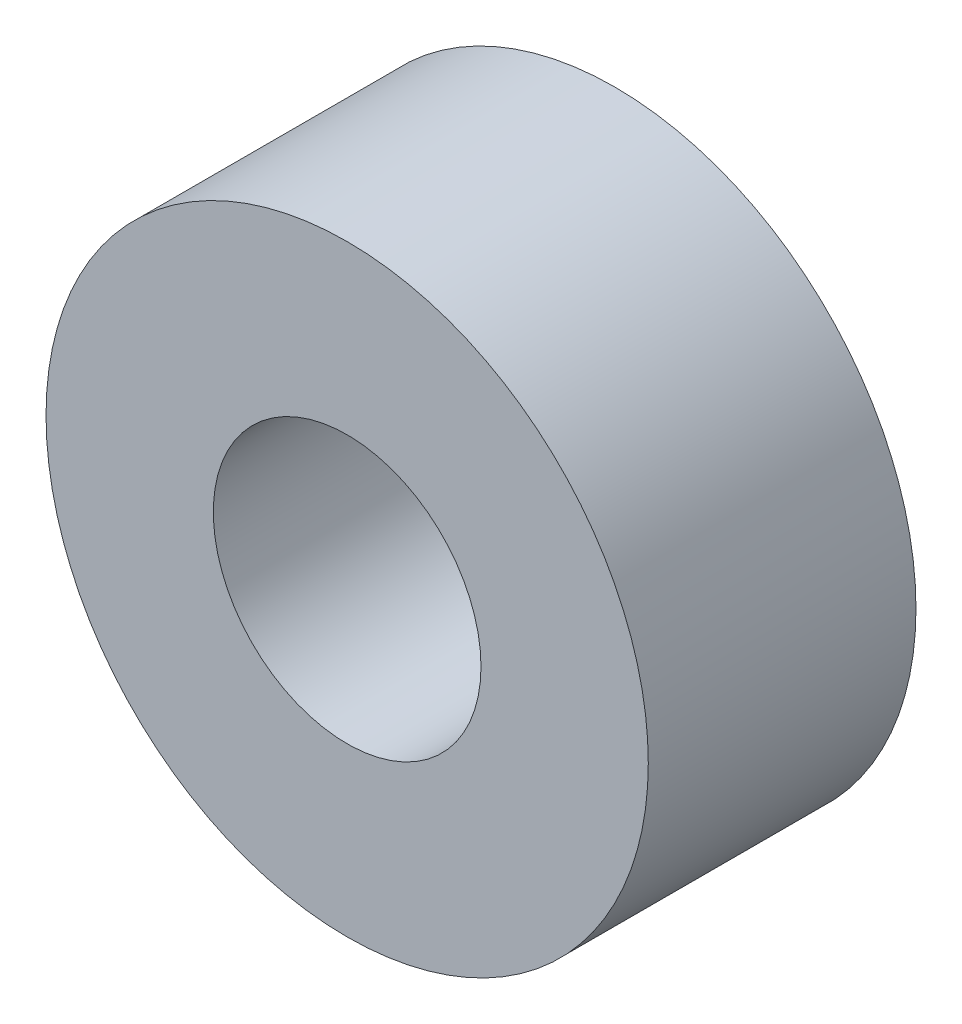
SolidWorks part; units mm, degrees
material "Alloy Steel (SS)"
ref_plane "Front Plane" through (0, 0, 0) normal (0, 0, 1) x (1, 0, 0)
ref_plane "Top Plane" through (0, 0, 0) normal (0, 1, 0) x (1, 0, 0)
ref_plane "Right Plane" through (0, 0, 0) normal (1, 0, 0) x (0, 0, -1)
sketch "Sketch1" plane through (0, 0, 0) normal (0, 0, 1) x (1, 0, 0)
  circle A0 centre (0, 0) radius 4.5
  circle A1 centre (0, 0) radius 2
  dimension "D1" = 9
  dimension "D2" = 4
extrude "Boss-Extrude1" add sketch "Sketch1" along normal blind 4
